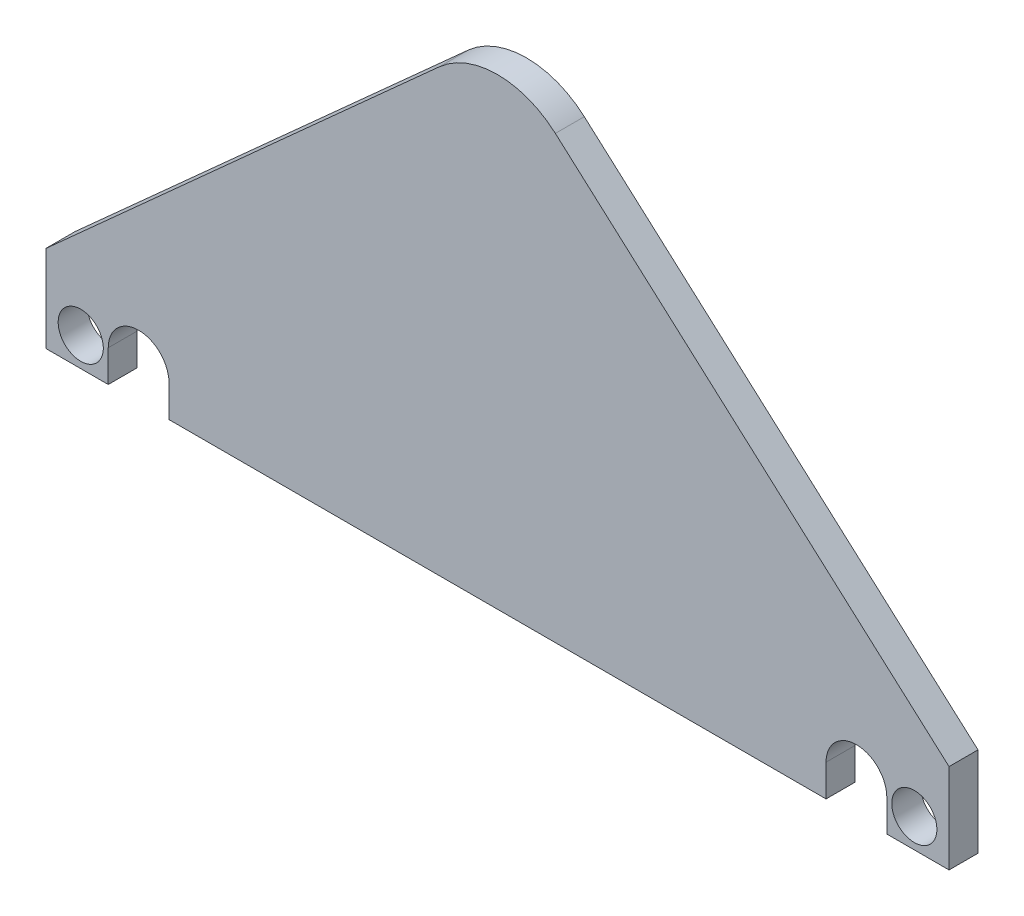
SolidWorks part; units mm, degrees
ref_plane "Front Plane" through (0, 0, 0) normal (0, 0, 1) x (1, 0, 0)
ref_plane "Top Plane" through (0, 0, 0) normal (0, 1, 0) x (1, 0, 0)
ref_plane "Right Plane" through (0, 0, 0) normal (1, 0, 0) x (0, 0, -1)
sketch "Sketch2" plane through (0, 0, -1125.8762) normal (0, 0, -1) x (-1, 0, 0)
  line L0 (78, 17.5) -> (78, 32.5)
  line L2 (-78, 17.5) -> (-78, 32.9695)
  line L4 (-78, 17.5) -> (-67.25, 17.5)
  line L6 (67.25, 17.5) -> (67.25, 23)
  line L7 (-78, 32.9695) -> (-9.9899, 93.6893)
  line L8 (78, 32.5) -> (10.0327, 93.651)
  line L10 (56.75, 23) -> (56.75, 17.5)
  line L11 (0, 78.3861) -> (0, 69.8604) construction
  line L12 (-67.25, 17.5) -> (-67.25, 23)
  line L13 (-56.75, 23) -> (-56.75, 17.5)
  line L14 (-56.75, 17.5) -> (56.75, 17.5)
  line L15 (67.25, 17.5) -> (78, 17.5)
  arc A0 (10.0327, 93.651) -> (-9.9899, 93.6893) centre (0, 82.5) ccw
  arc A1 (-67.25, 23) -> (-56.75, 23) centre (-62, 23) cw
  arc A2 (67.25, 23) -> (56.75, 23) centre (62, 23) ccw
  circle A4 centre (72, 22.5) radius 3.9
  circle A5 centre (-72, 22.5) radius 3.9
  point P16 (67.25, 20.25)
  point P19 (-67.25, 20.25)
  dimension "D7" = 30
  dimension "D2" = 15
  dimension "D6" = 5.5
  dimension "D8" = 10.5
  dimension "D9" = 5.5
extrude "Boss-Extrude1" add sketch "Sketch2" along normal blind 5
